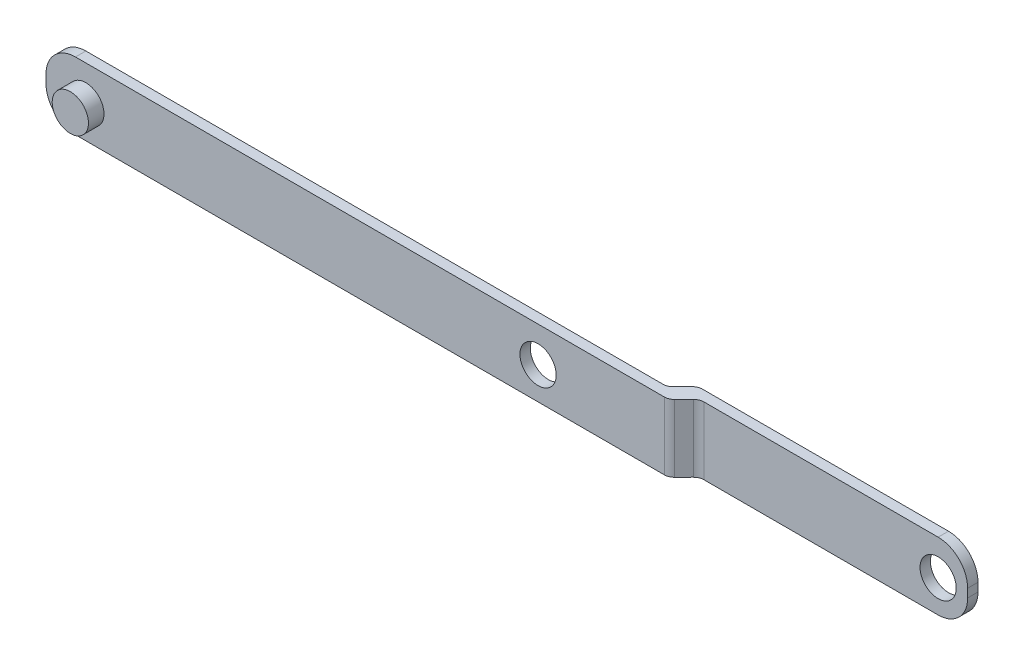
SolidWorks part; units mm, degrees
ref_plane "Front Plane" through (0, 0, 0) normal (0, 0, 1) x (1, 0, 0)
ref_plane "Top Plane" through (0, 0, 0) normal (0, 1, 0) x (1, 0, 0)
ref_plane "Right Plane" through (0, 0, 0) normal (1, 0, 0) x (0, 0, -1)
sketch "Sketch1" plane through (0, 0, 0) normal (0, 0, 1) x (1, 0, 0)
  line L0 (-104.732, 0) -> (104.732, 0) construction
  line L1 (0, 82.8902) -> (0, -82.8902) construction
  line L2 (1.1385, -6.2305) -> (82.16, -6.2365)
  line L3 (87.858, -0.5392) -> (87.8582, 1.0887)
  line L4 (82.1609, 6.7868) -> (8.3443, 6.7922)
  line L5 (8.3443, 6.7922) -> (-81.4437, 6.7988)
  line L6 (-87.1418, 1.1015) -> (-87.142, -0.5264)
  line L7 (-81.4447, -6.2245) -> (1.1385, -6.2305)
  arc A4 (82.16, -6.2365) -> (87.858, -0.5392) centre (82.1604, -0.5388) ccw
  arc A5 (87.8582, 1.0887) -> (82.1609, 6.7868) centre (82.1605, 1.0891) ccw
  arc A6 (-81.4437, 6.7988) -> (-87.1418, 1.1015) centre (-81.4442, 1.1011) ccw
  arc A7 (-87.142, -0.5264) -> (-81.4447, -6.2245) centre (-81.4443, -0.5268) ccw
  circle A10 centre (82.1604, 0) radius 3.5
  circle A11 centre (7.8931, 0) radius 3.5
  circle A12 centre (-79.4419, 0) radius 3.5
  point P4 (0, 0)
  point P8 (0, 0)
  point P12 (-87.1419, 0.2876)
  dimension "D1" = 5.6977
  dimension "D2" = 7
  dimension "D3" = 7.7
  dimension "D4" = 74.2673
  dimension "D5" = 7
  dimension "D6" = 7
extrude "Boss-Extrude6" add sketch "Sketch1" along normal blind 5 contours L2 A4 L3 A5 L4 L5 A6 L6 A7 L7 | A11 | A10
sketch "Sketch3" plane through (0, 0, 5) normal (0, 0, 1) x (1, 0, 0)
  circle A0 centre (-79.4419, 0) radius 3.5
sketch "Sketch4" plane through (0.0005, 6.7928, 0) normal (0.0001, 1, 0) x (1, -0.0001, 0)
  line L0 (0, -22.6631) -> (0, 22.6631) construction
  line L1 (-97.1882, 0) -> (-97.1882, -3)
  line L2 (144.1705, -2) -> (-144.1705, -2) construction
  line L3 (82.1604, -5) -> (-81.4442, -5) construction
  line L4 (-97.1882, -3) -> (30.8406, -3)
  line L6 (36.0756, -2) -> (33.1068, -5)
  line L7 (36.0756, -2) -> (91.1406, -2)
  line L8 (91.1406, -2) -> (91.1406, -5)
  line L9 (91.1406, -5) -> (33.1068, -5)
  line L11 (82.1604, 0) -> (-81.4442, 0) construction
  line L14 (-97.1882, 0) -> (33.8094, 0)
  line L15 (30.8406, -3) -> (33.8094, 0)
  point P4 (0, 0)
  point P8 (0, -2)
  dimension "D1" = 3
  dimension "D2" = 128.0288
  dimension "D3" = 4.2207
  dimension "D4" = 3
extrude "Cut-Extrude5" cut sketch "Sketch4" against normal through all
fillet "Fillet3" radius 2 4 edges at (36.0757, 0.2785, 2) (33.1068, 0.2788, 5) (33.8095, 0.2787, 0) (30.8406, 0.2789, 3)
extrude "Boss-Extrude9" add sketch "Sketch3" along normal blind 3
